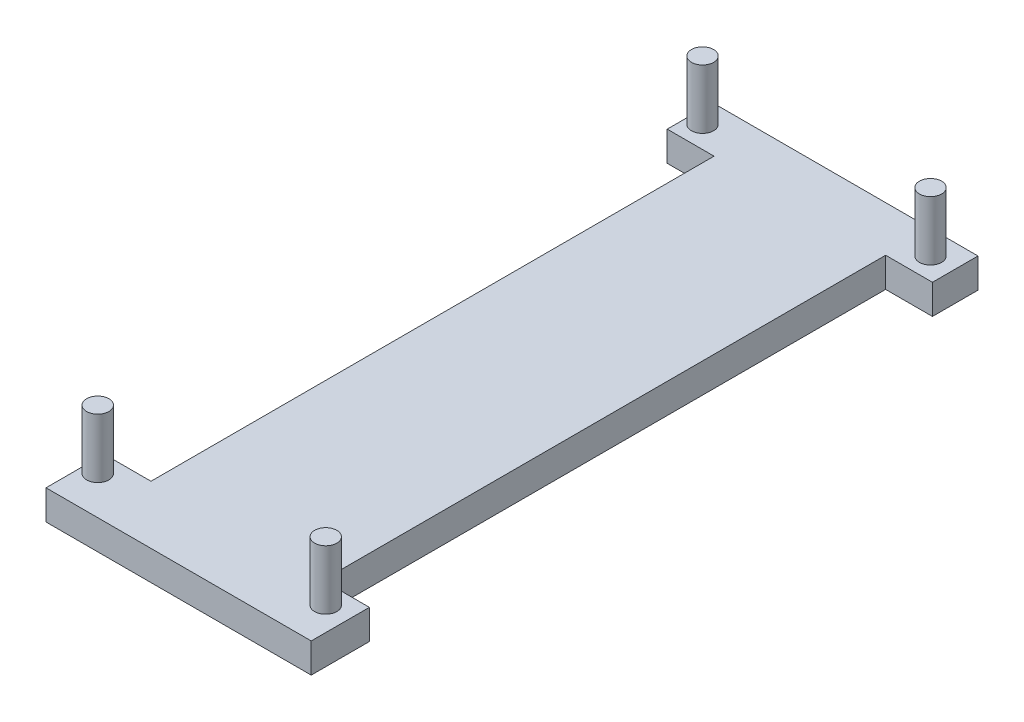
SolidWorks part; units mm, degrees
ref_plane "Front Plane" through (0, 0, 0) normal (0, 0, 1) x (1, 0, 0)
ref_plane "Top Plane" through (0, 0, 0) normal (0, 1, 0) x (1, 0, 0)
ref_plane "Right Plane" through (0, 0, 0) normal (1, 0, 0) x (0, 0, -1)
sketch "Sketch1" plane through (0, 0, 0) normal (0, 1, 0) x (1, 0, 0)
  line L2 (0, 0) -> (17.9, 0)
  line L3 (0, 0) -> (0, 45)
  line L4 (0, 45) -> (17.9, 45)
  line L5 (17.9, 0) -> (17.9, 45)
  dimension "D1" = 45
  dimension "D2" = 17.9
extrude "Boss-Extrude1" add sketch "Sketch1" along normal blind 2
sketch "Sketch2" plane through (0, 2, 0) normal (0, 1, 0) x (1, 0, 0)
  line L1 (14.74, 3.16) -> (17.9, 3.16) construction
  line L2 (14.74, 3.16) -> (14.74, 0) construction
  line L3 (14.74, 0) -> (17.9, 0) construction
  line L4 (17.9, 3.16) -> (17.9, 0) construction
  line L5 (17.9, 45) -> (14.74, 45) construction
  line L6 (17.9, 45) -> (17.9, 41.84) construction
  line L7 (17.9, 41.84) -> (14.74, 41.84) construction
  line L8 (14.74, 45) -> (14.74, 41.84) construction
  line L9 (0, 45) -> (3.16, 45) construction
  line L10 (0, 45) -> (0, 41.84) construction
  line L11 (0, 41.84) -> (3.16, 41.84) construction
  line L12 (3.16, 45) -> (3.16, 41.84) construction
  line L13 (0, 0) -> (3.16, 0) construction
  line L14 (0, 0) -> (0, 3.16) construction
  line L15 (0, 3.16) -> (3.16, 3.16) construction
  line L16 (3.16, 0) -> (3.16, 3.16) construction
  circle A0 centre (0.9131, 43.3966) radius 0.75
  circle A1 centre (16.3005, 43.3966) radius 0.75
  circle A2 centre (16.3005, 2.58) radius 0.75
  circle A3 centre (0.9131, 2.58) radius 0.75
  dimension "D9" = 1.5
  dimension "D10" = 1.5
  dimension "D11" = 1.5
  dimension "D12" = 1.5
  dimension "D1" = 3.16
  dimension "D2" = 3.16
  dimension "D3" = 3.16
  dimension "D4" = 3.16
  dimension "D5" = 3.16
  dimension "D6" = 3.16
  dimension "D7" = 3.16
  dimension "D8" = 3.16
extrude "Boss-Extrude2" add sketch "Sketch2" along normal blind 4
sketch "Sketch4" plane through (0, 2, 0) normal (0, 1, 0) x (1, 0, 0)
  line L0 (0, 41.9257) -> (3.16, 41.9257)
  line L1 (0, 41.9257) -> (0, 3.9257)
  line L2 (0, 3.9257) -> (3.16, 3.9257)
  line L3 (3.16, 41.9257) -> (3.16, 3.9257)
  line L4 (14.74, 41.9257) -> (17.9, 41.9257)
  line L5 (14.74, 41.9257) -> (14.74, 3.9257)
  line L6 (14.74, 3.9257) -> (17.9, 3.9257)
  line L7 (17.9, 41.9257) -> (17.9, 3.9257)
  line L8 (17.9, 0) -> (17.9, 45) construction
  line L9 (0, 45) -> (0, 0) construction
  point P12 (3.16, 4.1795)
  point P13 (17.9, 4.1795)
  point P14 (3.16, 3.5731)
  point P15 (3.16, 3.815)
  dimension "D1" = 3.16
  dimension "D2" = 3.16
  dimension "D3" = 38
  dimension "D4" = 38
extrude "Cut-Extrude1" cut sketch "Sketch4" against normal blind 3.5
